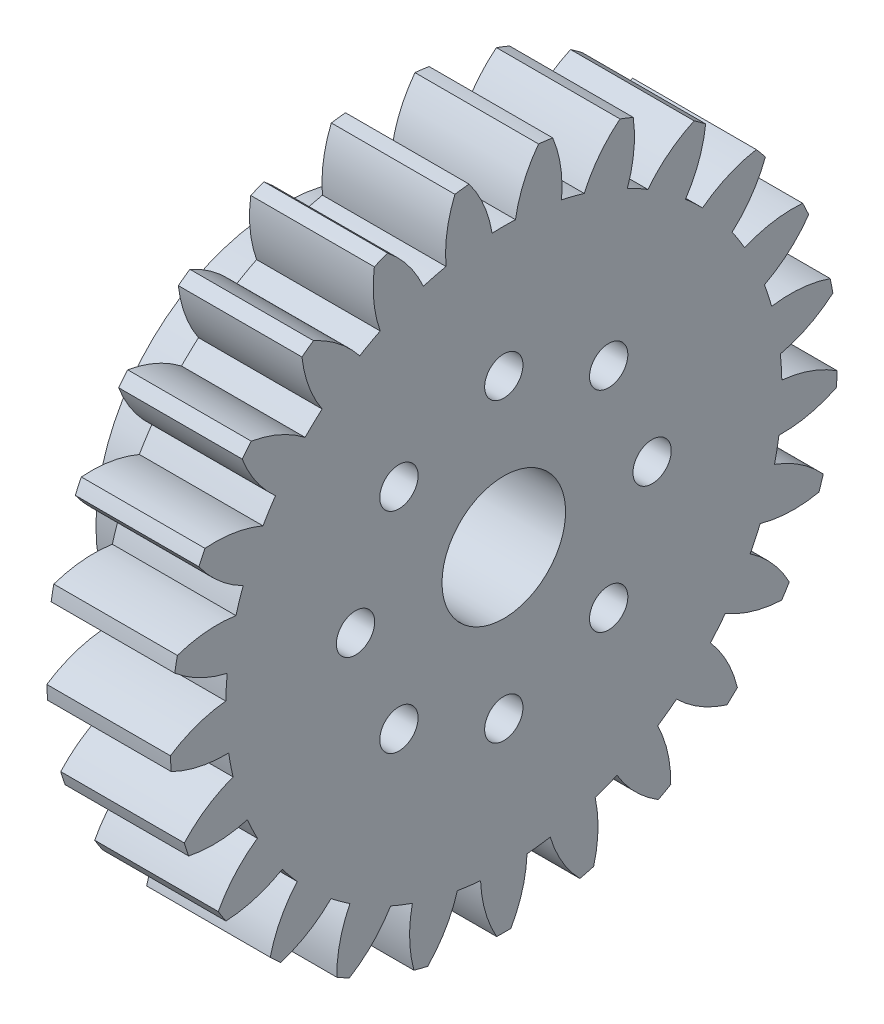
SolidWorks part; units mm, degrees
ref_plane "Plane1" through (0, 0, 0) normal (0, 0, 1) x (1, 0, 0)
ref_plane "Plane2" through (0, 0, 0) normal (0, 1, 0) x (1, 0, 0)
ref_plane "Plane3" through (0, 0, 0) normal (1, 0, 0) x (0, 0, -1)
other "Configuration Table"
sketch "HoldingSke" plane through (0, 0, 0) normal (0, 1, 0) x (1, 0, 0)
  line L0 (0, 0) -> (0.4532, -0.2113)
  line L1 (-15, 0) -> (100, 0) construction
  line L2 (0, 0) -> (-2.1039, 2.3779)
  line L3 (0, 0) -> (-11.863, 4.5341)
  line L4 (0, 0) -> (7.8269, 3.6497)
  line L5 (0, 0) -> (-46.8476, -17.4728)
  line L6 (0, 0) -> (-8.2896, -5.593)
  line L7 (-2.1039, 2.3779) -> (8.6586, 51.2059)
  line L8 (-76.2, 54.61) -> (-74.4, 54.61)
  line L9 (-71.009, 38.7566) -> (-53.1078, 45.2721)
  line L10 (-76.2, 71.12) -> (104.1128, 71.12)
  line L11 (0, 0) -> (-10, 0)
  line L12 (-76.2, 101.6) -> (-76.133, 101.6)
  line L13 (24.9733, 27.94) -> (52.9518, 28.4284)
  line L14 (24.9733, 27.94) -> (24.9743, 27.94)
  line L15 (24.9733, 27.94) -> (100.4006, 29.5858)
  line L16 (-63.627, -2) -> (-12.827, -2)
  circle A0 centre (0, 0) radius 5
  circle A1 centre (0, 0) radius 22.499
  circle A2 centre (0, 0) radius 37.5
  circle A3 centre (0, 0) radius 5
  dimension "MHD" = 44.998
  dimension "Hub_dia" = 75
  dimension "Bore" = 10
  dimension "MBD" = 10
  dimension "Num_teeth" = 25
  dimension "Pitch" = 0.5
  dimension "Overall_len" = 50
  dimension "Show_teeth" = 25
  dimension "Thickness" = 10
  dimension "OAL" = 50.0001
  dimension "T_dim" = 1.8
  dimension "Ap" = 20
  dimension "H" = 19.05
  dimension "Pitch_radius" = 180.3128
  dimension "Width" = 10
  dimension "Backlash" = 0.067
  dimension "Addendum_fac" = 1
  dimension "Dedendum_fac" = 1.25
  dimension "Clearance_fac" = 0.25
  dimension "Dedendum_add" = 0.001
  dimension "Module" = 2
sketch "BasProSke" plane through (0, 0, 0) normal (0, 1, 0) x (1, 0, 0)
  line L0 (-10, 0) -> (60, 0) construction
  line L1 (0, 0) -> (0, 27)
  line L2 (0, 0) -> (10, 0)
  line L3 (10, 0) -> (10, 27)
  line L4 (10, 27) -> (0, 27)
  dimension "Thickness" = 10
  dimension "Diameter" = 54
revolve "Base-Revolve" add sketch "BasProSke" angle 360 about L0
sketch "TooCutSke" plane through (0, 0, 0) normal (1, 0, 0) x (0, 0, -1)
  line L1 (0, 0) -> (0, 107) construction
  line L2 (0, 0) -> (-1.687, 24.943) construction
  line L3 (0, 0) -> (-6.2561, 49.5219) construction
  line L4 (-1.687, 24.943) -> (-3.128, 24.761) construction
  arc A0 (0.9462, 22.4791) -> (-0.9462, 22.4791) centre (0, 0) ccw
  arc A1 (2.8295, 26.8769) -> (-2.8295, 26.8769) centre (0, 0) ccw
  circle A2 centre (0, 0) radius 25 construction
  circle A3 centre (0, 0) radius 23.4923 construction
  arc A4 (-0.9462, 22.4791) -> (-2.8295, 26.8769) centre (-10.8135, 20.8556) ccw
  arc A5 (2.8295, 26.8769) -> (0.9462, 22.4791) centre (10.8135, 20.8556) ccw
  dimension "Root_dia" = 44.998
  dimension "Overcut_dia" = 54.0508
  dimension "Pitch_dia" = 50
  dimension "Base_dia" = 46.9846
  dimension "Flank_rad" = 10
  dimension "Half_ang" = 7.2
  dimension "Half_CT" = 1.4525
extrude "ToothCut" cut sketch "TooCutSke" along normal through all
fillet "Breaks" [suppressed] radius 0.04
fillet "RootFillets" [suppressed] radius 0.501
pattern_circular "TeethCuts" count 25 every 14.4 about axis through (-10, 0, 0) along (1, 0, 0) of "ToothCut", "RootFillets", "Breaks"
sketch "HubNeaOneSke" plane through (0, 0, 0) normal (-1, 0, 0) x (0, 0, 1)
  circle A0 centre (0, 0) radius 22.499
  dimension "Diameter" = 44.998
extrude "HubNearOne" [suppressed] add sketch "HubNeaOneSke" along normal blind 40.0001
sketch "HubNeaBotSke" plane through (0, 0, 0) normal (-1, 0, 0) x (0, 0, 1)
  circle A0 centre (0, 0) radius 22.499
  dimension "Diameter" = 44.998
extrude "HubNearBoth" [suppressed] add sketch "HubNeaBotSke" along normal blind 20
ref_plane "FarPln" through (10, 0, 0) normal (1, 0, 0) x (0, 0, -1)
sketch "HubFarSke" plane through (10, 0, 0) normal (1, 0, 0) x (0, 0, -1)
  circle A0 centre (0, 0) radius 22.499
  dimension "Diameter" = 44.998
extrude "HubFar" [suppressed] add sketch "HubFarSke" along normal blind 20
sketch "BorSke" plane through (0, 0, 0) normal (1, 0, 0) x (0, 0, -1)
  circle A0 centre (0, 0) radius 5
  dimension "Diameter" = 10
extrude "Bore" cut sketch "BorSke" along normal mid plane 100.0001
sketch "KeySke" plane through (0, 0, 0) normal (1, 0, 0) x (0, 0, -1)
  line L0 (-2, 0) -> (-2, 6.8)
  line L1 (-2, 6.8) -> (2, 6.8)
  line L2 (2, 6.8) -> (2, 0)
  line L3 (0, 0) -> (0, 34) construction
  line L4 (-2, 0) -> (2, 0)
  dimension "Offset" = 6.8
  dimension "Width" = 4
extrude "Keyway" [suppressed] cut sketch "KeySke" along normal mid plane 100.0001
pattern_circular "Keyway2" [suppressed] count 2 every 90 about axis through (-10, 0, 0) along (1, 0, 0)
sketch "Sketch2" plane through (0, 0, 0) normal (-1, 0, 0) x (0, 0, 1)
  line L0 (-5, 0) -> (5, 0) construction
  circle A0 centre (0, 0) radius 5 construction
  circle A1 centre (0, 0) radius 15
  dimension "D1" = 30
extrude "Boss-Extrude1" add sketch "Sketch2" along normal blind 8
sketch "Sketch3" plane through (-8, 0, 0) normal (-1, 0, 0) x (0, 0, 1)
  circle A0 centre (0, 0) radius 6
  dimension "D1" = 12
extrude "Cut-Extrude2" cut sketch "Sketch3" against normal up to surface (8 mm away) up to face at (0, 0, 5)
sketch "Sketch16" plane through (-8, 0, 0) normal (-1, 0, 0) x (0, 0, 1)
  line L0 (0, 0) -> (-12, 0) construction
  line L1 (0, 0) -> (12, 0) construction
  point P0 (12, 0)
  point P4 (8.4853, -8.4853)
  point P5 (0, -12)
  point P6 (-8.4853, -8.4853)
  point P7 (-12, 0)
  point P8 (-8.4853, 8.4853)
  point P9 (0, 12)
  point P10 (8.4853, 8.4853)
  point P11 (0, 0)
  dimension "D2" = 24
  dimension "D1" = 8
hole_wizard "CSK for M2.5 Flat Head Machine Screw1" positions "Sketch16" profile "Sketch17" countersink size "M2.5" standard "ANSI Metric"
sketch "Sketch17" plane through (-8, 0, 12) normal (0, 1, 0) x (0, 0, 1)
  line L0 (0, 0) -> (0, 18.9313)
  line L1 (0, 18.9313) -> (1.55, 18)
  line L2 (1.55, 18) -> (1.55, 1.2)
  line L3 (1.55, 1.2) -> (2.75, 0)
  line L5 (2.75, 0) -> (0, 0)
  line L6 (-1.55, 1.2) -> (-2.75, 0) construction
  line L10 (0, 18.9313) -> (-1.55, 18) construction
  line L11 (0, -6.35) -> (0, 107.95) construction
  dimension "Hole Dia." = 3.1
  dimension "Hole Depth" = 18
  dimension "Near C'Sink Dia." = 5.5
  dimension "Near C'Sink Angle" = 90
  dimension "Drill Angle" = 118
equation "' \"Module@HoldingSke\" = 6.35"
equation "' \"Num_teeth@HoldingSke\" = 12"
equation "' \"Ap@HoldingSke\" =  20"
equation "' \"Ap@HoldingSke\" = 20"
equation "' \"Width@HoldingSke\" = 0.5 * 25.4"
equation "' \"Hub_dia@HoldingSke\"= 1 * 25.4"
equation "' \"Hub_dia@HoldingSke\" = 1 * 25.4"
equation "' \"Overall_len@HoldingSke\" = 1.0 * 25.4"
equation "' \"Bore@HoldingSke\" = 0.75 * 25.4"
equation "' \"T_dim@HoldingSke\" = 0.1 * 25.4"
equation "' \"Width@KeySke\" = 0.25 * 25.4"
equation "' \"Show_teeth@HoldingSke\" = 13"
equation "' \"Backlash@HoldingSke\" = 0.009 * 25.4"
equation "' \"Addendum_fac@HoldingSke\" = 1.0"
equation "' \"Dedendum_fac@HoldingSke\" = 1.25"
equation "' \"Dedendum_add@HoldingSke\" = 0.00005 * 25.4"
equation "' \"Clearance_fac@HoldingSke\" = 0.25"
equation "\"Pitch@HoldingSke\" = 1 / \"Module@HoldingSke\""
equation "\"Overcut_dia@TooCutSke\" = (\"Num_teeth@HoldingSke\" + 2 * \"Addendum_fac@HoldingSke\") / \"Pitch@HoldingSke\" + 0.002 * 25.4"
equation "\"Pitch_dia@TooCutSke\" = \"Num_teeth@HoldingSke\" / \"Pitch@HoldingSke\""
equation "\"Base_dia@TooCutSke\" = \"Num_teeth@HoldingSke\" / \"Pitch@HoldingSke\" * cos((\"Ap@HoldingSke\"  * 3.14159265 / 180))"
equation "\"Root_dia@TooCutSke\" = (\"Num_teeth@HoldingSke\" + 2) / \"Pitch@HoldingSke\" - 2 * (\"Addendum_fac@HoldingSke\" + \"Dedendum_fac@HoldingSke\") / \"Pitch@HoldingSke\" - \"Dedendum_add@HoldingSke\" * 2"
equation "\"Half_ang@TooCutSke\" = 180 / \"Num_teeth@HoldingSke\""
equation "\"Half_CT@TooCutSke\" = \"Num_teeth@HoldingSke\" / \"Pitch@HoldingSke\" * sin((3.14159265 / 2 / \"Num_teeth@HoldingSke\")) / 2 - 7 * \"Backlash@HoldingSke\" / 4"
equation "\"Flank_rad@TooCutSke\" = \"Num_teeth@HoldingSke\" / \"Pitch@HoldingSke\" / 5"
equation "\"Radius@RootFillets\" = \"Clearance_fac@HoldingSke\" / \"Pitch@HoldingSke\" + \"Dedendum_add@HoldingSke\""
equation "\"Break_rad@Breaks\" = 0.02 / \"Pitch@HoldingSke\""
equation "\"Thickness@HoldingSke\" = \"Width@HoldingSke\""
equation "\"OAL@HoldingSke\" = \"Thickness@HoldingSke\""
equation "\"MHD@HoldingSke\" = (\"Num_teeth@HoldingSke\" + 2) / \"Pitch@HoldingSke\" - 2 * (\"Addendum_fac@HoldingSke\" + \"Dedendum_fac@HoldingSke\")  / \"Pitch@HoldingSke\" - \"Dedendum_add@HoldingSke\" * 2"
equation "\"MBD@HoldingSke\" = (\"Num_teeth@HoldingSke\" + 2) / \"Pitch@HoldingSke\" - 2 * (\"Addendum_fac@HoldingSke\" + \"Dedendum_fac@HoldingSke\")  / \"Pitch@HoldingSke\" - \"Dedendum_add@HoldingSke\" * 2 - 0.002 * 25.4"
equation "\"MHD@HoldingSke\" = ((sgn( \"MHD@HoldingSke\" - \"Hub_dia@HoldingSke\" )-1)*( \"MHD@HoldingSke\" - \"Hub_dia@HoldingSke\" ))/-2+ \"Hub_dia@HoldingSke\""
equation "\"MBD@HoldingSke\" = ((sgn( \"MBD@HoldingSke\" - \"Bore@HoldingSke\" )-1)*( \"MBD@HoldingSke\" - \"Bore@HoldingSke\" ))/-2+ \"Bore@HoldingSke\""
equation "\"OAL@HoldingSke\" = ((sgn( \"OAL@HoldingSke\" - \"Overall_len@HoldingSke\" )+1)*( \"OAL@HoldingSke\" - \"Overall_len@HoldingSke\" ))/2 + \"Overall_len@HoldingSke\" + 0.000002 * 25.4"
equation "\"Num_teeth@TeethCuts\" = int( \"Show_teeth@HoldingSke\" ) + 1"
equation "\"Num_teeth@TeethCuts\" = ((sgn( \"Num_teeth@TeethCuts\" - \"Num_teeth@HoldingSke\" )-1)*( \"Num_teeth@TeethCuts\" - \"Num_teeth@HoldingSke\" ))/-2+ \"Num_teeth@HoldingSke\""
equation "\"Num_teeth@TeethCuts\" = ((sgn( \"Num_teeth@TeethCuts\" - 2.0)+1)*( \"Num_teeth@TeethCuts\" - 2.0))/2 +2.0"
equation "\"Angle@TeethCuts\" = 360.0 / \"Num_teeth@HoldingSke\""
equation "\"Diameter@BasProSke\" = (\"Num_teeth@HoldingSke\" + 2 * \"Addendum_fac@HoldingSke\") / \"Pitch@HoldingSke\""
equation "\"Thickness@BasProSke\"  = \"Thickness@HoldingSke\""
equation "' \"Fillet_rad@BasProSke\" =  \"Thickness@HoldingSke\" * 0.05"
equation "' \"Fillet_rad@BasProSke\" = \"Thickness@HoldingSke\" * 0.05"
equation "\"MHD@HoldingSke\" = ((sgn( \"MHD@HoldingSke\" - \"Root_dia@TooCutSke\" )-1)*( \"MHD@HoldingSke\" - \"Root_dia@TooCutSke\" ))/-2+ \"Root_dia@TooCutSke\""
equation "\"Diameter@HubNeaOneSke\" = \"MHD@HoldingSke\""
equation "\"Length@HubNearOne\" = \"OAL@HoldingSke\" - \"Thickness@BasProSke\""
equation "\"Diameter@HubNeaBotSke\" = \"MHD@HoldingSke\""
equation "\"Length@HubNearBoth\" = ( \"OAL@HoldingSke\" - \"Thickness@BasProSke\" ) / 2.0"
equation "\"Thickness@FarPln\" = \"Thickness@BasProSke\""
equation "\"Diameter@HubFarSke\" = \"MHD@HoldingSke\""
equation "\"Length@HubFar\" = ( \"OAL@HoldingSke\" - \"Thickness@BasProSke\" ) / 2.0"
equation "\"Diameter@BorSke\" = \"MBD@HoldingSke\""
equation "\"D1@Bore\" = \"OAL@HoldingSke\" * 2.0"
equation "\"D1@Keyway\" = \"OAL@HoldingSke\" * 2.0"
equation "\"Offset@KeySke\" = \"T_dim@HoldingSke\" + \"MBD@HoldingSke\" / 2.0"
